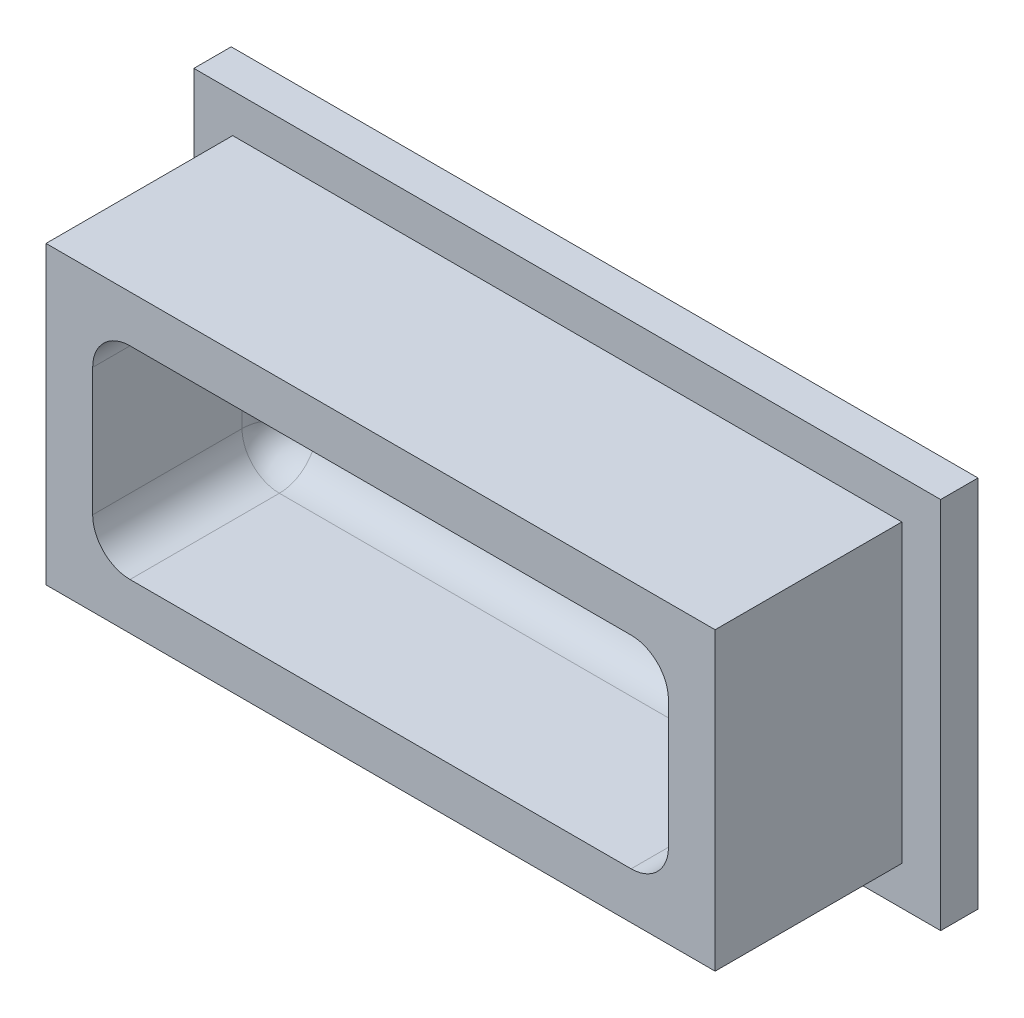
SolidWorks part; units mm, degrees
ref_plane "Front Plane" through (0, 0, 0) normal (0, 0, 1) x (1, 0, 0)
ref_plane "Top Plane" through (0, 0, 0) normal (0, 1, 0) x (1, 0, 0)
ref_plane "Right Plane" through (0, 0, 0) normal (1, 0, 0) x (0, 0, -1)
sketch "Sketch1" plane through (0, 0, 0) normal (0, 0, 1) x (1, 0, 0)
  line L1 (-20, -10) -> (20, -10)
  line L2 (-20, -10) -> (-20, 10)
  line L3 (-20, 10) -> (20, 10)
  line L4 (20, -10) -> (20, 10)
  line L5 (-20, -10) -> (20, 10) construction
  line L6 (-20, 10) -> (20, -10) construction
  point P0 (0, 0)
  dimension "D1" = 20
  dimension "D2" = 40
extrude "Boss-Extrude1" add sketch "Sketch1" along normal blind 2
sketch "Sketch2" plane through (0, 0, 2) normal (0, 0, 1) x (1, 0, 0)
  line L16 (-17.92, -7.92) -> (17.92, -7.92)
  line L17 (17.92, -7.92) -> (17.92, 7.92)
  line L18 (17.92, 7.92) -> (-17.92, 7.92)
  line L19 (-17.92, 7.92) -> (-17.92, -7.92)
  line L20 (-17.92, -7.92) -> (17.92, -7.92)
  line L21 (17.92, -7.92) -> (17.92, 7.92)
  line L22 (17.92, 7.92) -> (-17.92, 7.92)
  line L23 (-17.92, 7.92) -> (-17.92, -7.92)
  dimension "D1" = 2.08
extrude "Boss-Extrude2" add sketch "Sketch2" along normal blind 10
sketch "Sketch4" plane through (0, 0, 12) normal (0, 0, 1) x (1, 0, 0)
  line L8 (-15.42, 5.42) -> (-15.42, -5.42)
  line L9 (-15.42, -5.42) -> (15.42, -5.42)
  line L10 (15.42, -5.42) -> (15.42, 5.42)
  line L11 (15.42, 5.42) -> (-15.42, 5.42)
  line L12 (-15.42, 5.42) -> (-15.42, -5.42)
  line L13 (-15.42, -5.42) -> (15.42, -5.42)
  line L14 (15.42, -5.42) -> (15.42, 5.42)
  line L15 (15.42, 5.42) -> (-15.42, 5.42)
  dimension "D1" = 2.5
extrude "Cut-Extrude1" cut sketch "Sketch4" against normal up to surface (10 mm away) up to face at (0, 0, 2)
fillet "Fillet1" radius 2 8 edges at (15.42, 0, 2) (0, -5.42, 2) (-15.42, 0, 2) (0, 5.42, 2) (15.42, 5.42, 7) (15.42, -5.42, 7) (-15.42, -5.42, 7) (-15.42, 5.42, 7)
